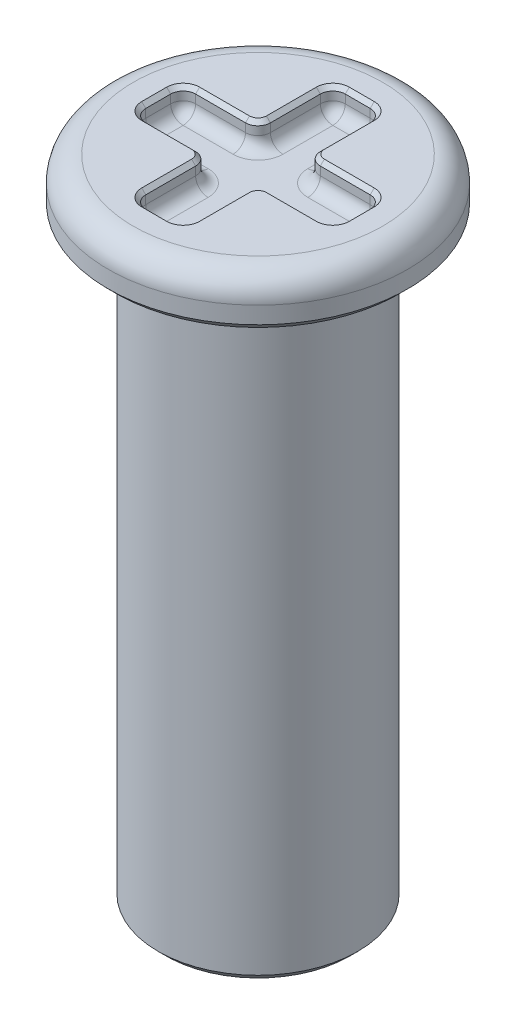
SolidWorks part; units mm, degrees
ref_plane "Front Plane" through (0, 0, 0) normal (0, 0, 1) x (1, 0, 0)
ref_plane "Top Plane" through (0, 0, 0) normal (0, 1, 0) x (1, 0, 0)
ref_plane "Right Plane" through (0, 0, 0) normal (1, 0, 0) x (0, 0, -1)
sketch "Sketch1" plane through (0, 0, 0) normal (0, 0, 1) x (1, 0, 0)
  line L0 (0, 3.6554) -> (0, -3.5835) construction
  line L1 (2.3813, 0) -> (3.175, 0)
  line L2 (3.175, 0) -> (3.175, 19.05)
  line L3 (3.175, 19.05) -> (4.7625, 19.05)
  line L4 (4.7625, 19.05) -> (4.7625, 20.6375)
  line L5 (4.7625, 20.6375) -> (0, 20.6375)
  line L6 (2.3812, 19.05) -> (0, 19.05)
  line L7 (0, 20.6375) -> (0, 19.05)
  line L8 (2.3812, 19.05) -> (2.3813, 0)
  dimension "D1" = 6.35
  dimension "D2" = 4.7625
  dimension "D3" = 19.05
  dimension "D4" = 1.5875
  dimension "D5" = 9.525
revolve "Revolve1" add sketch "Sketch1" angle 360 about L0
sketch "Sketch2" plane through (0, 20.6375, 0) normal (0, 1, 0) x (1, 0, 0)
  line L0 (-3.175, 0.7937) -> (-3.175, -0.7938)
  line L1 (-3.175, -0.7938) -> (-0.7938, -0.7937)
  line L2 (-0.7938, -0.7937) -> (-0.7938, -3.175)
  line L3 (-0.7938, -3.175) -> (0.7937, -3.175)
  line L4 (0.7937, -3.175) -> (0.7938, -0.7937)
  line L5 (0.7938, -0.7937) -> (3.175, -0.7937)
  line L6 (3.175, -0.7937) -> (3.175, 0.7938)
  line L7 (3.175, 0.7938) -> (0.7938, 0.7937)
  line L8 (0.7938, 0.7937) -> (0.7937, 3.175)
  line L9 (0.7937, 3.175) -> (-0.7937, 3.175)
  line L10 (-0.7937, 3.175) -> (-0.7938, 0.7937)
  line L11 (-0.7938, 0.7937) -> (-3.175, 0.7937)
  line L12 (-3.175, 0) -> (3.175, 0) construction
  line L13 (0, -3.175) -> (0, 3.175) construction
  dimension "D1" = 6.35
  dimension "D2" = 1.5875
extrude "Cut-Extrude1" cut sketch "Sketch2" against normal blind 0.7937 contours L10 L11 L0 L1 L2 L3 L4 L5 L6 L7 L8 L9
fillet "Fillet1" radius 0.7937 2 edges at (-3.175, 19.05, 0) (-4.7625, 20.6375, 0)
fillet "Fillet2" radius 0.3969 25 edges at (0, 19.8438, -3.175) (-0.7938, 19.8438, -1.9844) (-3.175, 19.8438, 0) (-1.9844, 19.8438, 0.7938) (-0.7938, 19.8438, 1.9844) (0, 19.8438, 3.175) (0.7937, 19.8438, 1.9844) (1.9844, 19.8438, 0.7937) (3.175, 19.8438, 0) (1.9844, 19.8438, -0.7937) (0.7937, 19.8438, -1.9844) (-0.7938, 20.2406, -3.175) (-0.7938, 20.2406, -0.7937) (-3.175, 20.2406, -0.7937) (-3.175, 20.2406, 0.7938) (-0.7938, 20.2406, 0.7937) (-0.7938, 20.2406, 3.175) (0.7937, 20.2406, 3.175) (0.7937, 20.2406, 0.7937) (3.175, 20.2406, 0.7937) (3.175, 20.2406, -0.7938) (0.7937, 20.2406, -0.7937) (0.7937, 20.2406, -3.175) (-1.9844, 19.8438, -0.7937) (-2.3813, 19.05, 0)
chamfer "Chamfer1" distance 0.254 angle 45 3 edges at (-2.3812, 0, 0) (-3.175, 0, 0) (-4.7625, 19.05, 0)
chamfer "Chamfer2" distance 0.127 angle 45 24 edges at (-1.9844, 20.6375, -0.7937) (-3.0588, 20.6375, -0.6775) (-0.91, 20.6375, -0.91) (-0.7938, 20.6375, -1.9844) (-0.6775, 20.6375, -3.0588) (-3.0588, 20.6375, 0.6775) (-1.9844, 20.6375, 0.7938) (-0.91, 20.6375, 0.91) (0.6775, 20.6375, -3.0588) (-0.7938, 20.6375, 1.9844) (0.7937, 20.6375, -1.9844) (-0.6775, 20.6375, 3.0588) (0.91, 20.6375, -0.91) (1.9844, 20.6375, -0.7937) (3.0588, 20.6375, -0.6775) (0.6775, 20.6375, 3.0588) (0.7937, 20.6375, 1.9844) (0.91, 20.6375, 0.91) (3.0588, 20.6375, 0.6775) (1.9844, 20.6375, 0.7937) (-3.175, 20.6375, 0) (0, 20.6375, -3.175) (0, 20.6375, 3.175) (3.175, 20.6375, 0)
